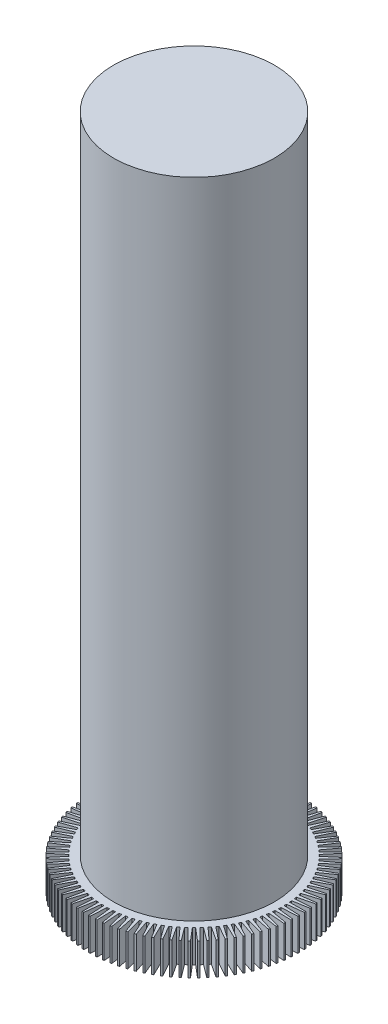
SolidWorks part; units mm, degrees
ref_plane "Front Plane" through (0, 0, 0) normal (0, 0, 1) x (1, 0, 0)
ref_plane "Top Plane" through (0, 0, 0) normal (0, 1, 0) x (1, 0, 0)
ref_plane "Right Plane" through (0, 0, 0) normal (1, 0, 0) x (0, 0, -1)
sketch "Sketch1" plane through (0, 0, 0) normal (0, 1, 0) x (1, 0, 0)
  line L0 (-0.05, 2.7495) -> (0.05, 2.7495) construction
  line L1 (0, 3.2495) -> (0, 2.2495) construction
  line L2 (-0.025, 3.2495) -> (-0.05, 2.7495)
  line L3 (0.025, 3.2495) -> (0.05, 2.7495)
  line L4 (-0.025, 3.2495) -> (0.025, 3.2495)
  line L5 (0.1791, 3.2447) -> (0.1227, 2.7473)
  line L6 (0.1791, 3.2447) -> (0.229, 3.2416)
  line L7 (0.229, 3.2416) -> (0.2225, 2.741)
  line L8 (0.3825, 3.2271) -> (0.295, 2.7341)
  line L9 (0.3825, 3.2271) -> (0.4321, 3.2208)
  line L10 (0.4321, 3.2208) -> (0.3942, 2.7216)
  line L11 (0.5843, 3.1967) -> (0.4661, 2.7102)
  line L12 (0.5843, 3.1967) -> (0.6335, 3.1873)
  line L13 (0.6335, 3.1873) -> (0.5643, 2.6915)
  line L14 (0.7839, 3.1537) -> (0.6354, 2.6756)
  line L15 (0.7839, 3.1537) -> (0.8323, 3.1412)
  line L16 (0.8323, 3.1412) -> (0.7322, 2.6507)
  line L17 (0.9804, 3.0982) -> (0.8021, 2.6304)
  line L18 (0.9804, 3.0982) -> (1.0279, 3.0828)
  line L19 (1.0279, 3.0828) -> (0.8972, 2.5995)
  line L20 (1.173, 3.0306) -> (0.9657, 2.5749)
  line L21 (1.173, 3.0306) -> (1.2195, 3.0121)
  line L22 (1.2195, 3.0121) -> (1.0587, 2.5381)
  line L23 (1.361, 2.9509) -> (1.1255, 2.5092)
  line L24 (1.361, 2.9509) -> (1.4062, 2.9296)
  line L25 (1.4062, 2.9296) -> (1.2159, 2.4666)
  line L26 (1.5436, 2.8596) -> (1.2808, 2.4335)
  line L27 (1.5436, 2.8596) -> (1.5874, 2.8356)
  line L28 (1.5874, 2.8356) -> (1.3684, 2.3854)
  line L29 (1.7201, 2.7571) -> (1.4311, 2.3483)
  line L30 (1.7201, 2.7571) -> (1.7623, 2.7303)
  line L31 (1.7623, 2.7303) -> (1.5155, 2.2947)
  line L32 (1.8898, 2.6436) -> (1.5757, 2.2538)
  line L33 (1.8898, 2.6436) -> (1.9303, 2.6142)
  line L34 (1.9303, 2.6142) -> (1.6566, 2.195)
  line L35 (2.0521, 2.5198) -> (1.7141, 2.1504)
  line L36 (2.0521, 2.5198) -> (2.0906, 2.4879)
  line L37 (2.0906, 2.4879) -> (1.7912, 2.0867)
  line L38 (2.2062, 2.3859) -> (1.8457, 2.0386)
  line L39 (2.2062, 2.3859) -> (2.2427, 2.3517)
  line L40 (2.2427, 2.3517) -> (1.9186, 1.9701)
  line L41 (2.3517, 2.2427) -> (1.9701, 1.9186)
  line L42 (2.3517, 2.2427) -> (2.3859, 2.2062)
  line L43 (2.3859, 2.2062) -> (2.0386, 1.8457)
  line L44 (2.4879, 2.0906) -> (2.0867, 1.7912)
  line L45 (2.4879, 2.0906) -> (2.5198, 2.0521)
  line L46 (2.5198, 2.0521) -> (2.1504, 1.7141)
  line L47 (2.6142, 1.9303) -> (2.195, 1.6566)
  line L48 (2.6142, 1.9303) -> (2.6436, 1.8898)
  line L49 (2.6436, 1.8898) -> (2.2538, 1.5757)
  line L50 (2.7303, 1.7623) -> (2.2947, 1.5155)
  line L51 (2.7303, 1.7623) -> (2.7571, 1.7201)
  line L52 (2.7571, 1.7201) -> (2.3483, 1.4311)
  line L53 (2.8356, 1.5874) -> (2.3854, 1.3684)
  line L54 (2.8356, 1.5874) -> (2.8596, 1.5436)
  line L55 (2.8596, 1.5436) -> (2.4335, 1.2808)
  line L56 (2.9296, 1.4062) -> (2.4666, 1.2159)
  line L57 (2.9296, 1.4062) -> (2.9509, 1.361)
  line L58 (2.9509, 1.361) -> (2.5092, 1.1255)
  line L59 (3.0121, 1.2195) -> (2.5381, 1.0587)
  line L60 (3.0121, 1.2195) -> (3.0306, 1.173)
  line L61 (3.0306, 1.173) -> (2.5749, 0.9657)
  line L62 (3.0828, 1.0279) -> (2.5995, 0.8972)
  line L63 (3.0828, 1.0279) -> (3.0982, 0.9804)
  line L64 (3.0982, 0.9804) -> (2.6304, 0.8021)
  line L65 (3.1412, 0.8323) -> (2.6507, 0.7322)
  line L66 (3.1412, 0.8323) -> (3.1537, 0.7839)
  line L67 (3.1537, 0.7839) -> (2.6756, 0.6354)
  line L68 (3.1873, 0.6335) -> (2.6915, 0.5643)
  line L69 (3.1873, 0.6335) -> (3.1967, 0.5843)
  line L70 (3.1967, 0.5843) -> (2.7102, 0.4661)
  line L71 (3.2208, 0.4321) -> (2.7216, 0.3942)
  line L72 (3.2208, 0.4321) -> (3.2271, 0.3825)
  line L73 (3.2271, 0.3825) -> (2.7341, 0.295)
  line L74 (3.2416, 0.229) -> (2.741, 0.2225)
  line L75 (3.2416, 0.229) -> (3.2447, 0.1791)
  line L76 (3.2447, 0.1791) -> (2.7473, 0.1227)
  line L77 (3.2495, 0.025) -> (2.7495, 0.05)
  line L78 (3.2495, 0.025) -> (3.2495, -0.025)
  line L79 (3.2495, -0.025) -> (2.7495, -0.05)
  line L80 (3.2447, -0.1791) -> (2.7473, -0.1227)
  line L81 (3.2447, -0.1791) -> (3.2416, -0.229)
  line L82 (3.2416, -0.229) -> (2.741, -0.2225)
  line L83 (3.2271, -0.3825) -> (2.7341, -0.295)
  line L84 (3.2271, -0.3825) -> (3.2208, -0.4321)
  line L85 (3.2208, -0.4321) -> (2.7216, -0.3942)
  line L86 (3.1967, -0.5843) -> (2.7102, -0.4661)
  line L87 (3.1967, -0.5843) -> (3.1873, -0.6335)
  line L88 (3.1873, -0.6335) -> (2.6915, -0.5643)
  line L89 (3.1537, -0.7839) -> (2.6756, -0.6354)
  line L90 (3.1537, -0.7839) -> (3.1412, -0.8323)
  line L91 (3.1412, -0.8323) -> (2.6507, -0.7322)
  line L92 (3.0982, -0.9804) -> (2.6304, -0.8021)
  line L93 (3.0982, -0.9804) -> (3.0828, -1.0279)
  line L94 (3.0828, -1.0279) -> (2.5995, -0.8972)
  line L95 (3.0306, -1.173) -> (2.5749, -0.9657)
  line L96 (3.0306, -1.173) -> (3.0121, -1.2195)
  line L97 (3.0121, -1.2195) -> (2.5381, -1.0587)
  line L98 (2.9509, -1.361) -> (2.5092, -1.1255)
  line L99 (2.9509, -1.361) -> (2.9296, -1.4062)
  line L100 (2.9296, -1.4062) -> (2.4666, -1.2159)
  line L101 (2.8596, -1.5436) -> (2.4335, -1.2808)
  line L102 (2.8596, -1.5436) -> (2.8356, -1.5874)
  line L103 (2.8356, -1.5874) -> (2.3854, -1.3684)
  line L104 (2.7571, -1.7201) -> (2.3483, -1.4311)
  line L105 (2.7571, -1.7201) -> (2.7303, -1.7623)
  line L106 (2.7303, -1.7623) -> (2.2947, -1.5155)
  line L107 (2.6436, -1.8898) -> (2.2538, -1.5757)
  line L108 (2.6436, -1.8898) -> (2.6142, -1.9303)
  line L109 (2.6142, -1.9303) -> (2.195, -1.6566)
  line L110 (2.5198, -2.0521) -> (2.1504, -1.7141)
  line L111 (2.5198, -2.0521) -> (2.4879, -2.0906)
  line L112 (2.4879, -2.0906) -> (2.0867, -1.7912)
  line L113 (2.3859, -2.2062) -> (2.0386, -1.8457)
  line L114 (2.3859, -2.2062) -> (2.3517, -2.2427)
  line L115 (2.3517, -2.2427) -> (1.9701, -1.9186)
  line L116 (2.2427, -2.3517) -> (1.9186, -1.9701)
  line L117 (2.2427, -2.3517) -> (2.2062, -2.3859)
  line L118 (2.2062, -2.3859) -> (1.8457, -2.0386)
  line L119 (2.0906, -2.4879) -> (1.7912, -2.0867)
  line L120 (2.0906, -2.4879) -> (2.0521, -2.5198)
  line L121 (2.0521, -2.5198) -> (1.7141, -2.1504)
  line L122 (1.9303, -2.6142) -> (1.6566, -2.195)
  line L123 (1.9303, -2.6142) -> (1.8898, -2.6436)
  line L124 (1.8898, -2.6436) -> (1.5757, -2.2538)
  line L125 (1.7623, -2.7303) -> (1.5155, -2.2947)
  line L126 (1.7623, -2.7303) -> (1.7201, -2.7571)
  line L127 (1.7201, -2.7571) -> (1.4311, -2.3483)
  line L128 (1.5874, -2.8356) -> (1.3684, -2.3854)
  line L129 (1.5874, -2.8356) -> (1.5436, -2.8596)
  line L130 (1.5436, -2.8596) -> (1.2808, -2.4335)
  line L131 (1.4062, -2.9296) -> (1.2159, -2.4666)
  line L132 (1.4062, -2.9296) -> (1.361, -2.9509)
  line L133 (1.361, -2.9509) -> (1.1255, -2.5092)
  line L134 (1.2195, -3.0121) -> (1.0587, -2.5381)
  line L135 (1.2195, -3.0121) -> (1.173, -3.0306)
  line L136 (1.173, -3.0306) -> (0.9657, -2.5749)
  line L137 (1.0279, -3.0828) -> (0.8972, -2.5995)
  line L138 (1.0279, -3.0828) -> (0.9804, -3.0982)
  line L139 (0.9804, -3.0982) -> (0.8021, -2.6304)
  line L140 (0.8323, -3.1412) -> (0.7322, -2.6507)
  line L141 (0.8323, -3.1412) -> (0.7839, -3.1537)
  line L142 (0.7839, -3.1537) -> (0.6354, -2.6756)
  line L143 (0.6335, -3.1873) -> (0.5643, -2.6915)
  line L144 (0.6335, -3.1873) -> (0.5843, -3.1967)
  line L145 (0.5843, -3.1967) -> (0.4661, -2.7102)
  line L146 (0.4321, -3.2208) -> (0.3942, -2.7216)
  line L147 (0.4321, -3.2208) -> (0.3825, -3.2271)
  line L148 (0.3825, -3.2271) -> (0.295, -2.7341)
  line L149 (0.229, -3.2416) -> (0.2225, -2.741)
  line L150 (0.229, -3.2416) -> (0.1791, -3.2447)
  line L151 (0.1791, -3.2447) -> (0.1227, -2.7473)
  line L152 (0.025, -3.2495) -> (0.05, -2.7495)
  line L153 (0.025, -3.2495) -> (-0.025, -3.2495)
  line L154 (-0.025, -3.2495) -> (-0.05, -2.7495)
  line L155 (-0.1791, -3.2447) -> (-0.1227, -2.7473)
  line L156 (-0.1791, -3.2447) -> (-0.229, -3.2416)
  line L157 (-0.229, -3.2416) -> (-0.2225, -2.741)
  line L158 (-0.3825, -3.2271) -> (-0.295, -2.7341)
  line L159 (-0.3825, -3.2271) -> (-0.4321, -3.2208)
  line L160 (-0.4321, -3.2208) -> (-0.3942, -2.7216)
  line L161 (-0.5843, -3.1967) -> (-0.4661, -2.7102)
  line L162 (-0.5843, -3.1967) -> (-0.6335, -3.1873)
  line L163 (-0.6335, -3.1873) -> (-0.5643, -2.6915)
  line L164 (-0.7839, -3.1537) -> (-0.6354, -2.6756)
  line L165 (-0.7839, -3.1537) -> (-0.8323, -3.1412)
  line L166 (-0.8323, -3.1412) -> (-0.7322, -2.6507)
  line L167 (-0.9804, -3.0982) -> (-0.8021, -2.6304)
  line L168 (-0.9804, -3.0982) -> (-1.0279, -3.0828)
  line L169 (-1.0279, -3.0828) -> (-0.8972, -2.5995)
  line L170 (-1.173, -3.0306) -> (-0.9657, -2.5749)
  line L171 (-1.173, -3.0306) -> (-1.2195, -3.0121)
  line L172 (-1.2195, -3.0121) -> (-1.0587, -2.5381)
  line L173 (-1.361, -2.9509) -> (-1.1255, -2.5092)
  line L174 (-1.361, -2.9509) -> (-1.4062, -2.9296)
  line L175 (-1.4062, -2.9296) -> (-1.2159, -2.4666)
  line L176 (-1.5436, -2.8596) -> (-1.2808, -2.4335)
  line L177 (-1.5436, -2.8596) -> (-1.5874, -2.8356)
  line L178 (-1.5874, -2.8356) -> (-1.3684, -2.3854)
  line L179 (-1.7201, -2.7571) -> (-1.4311, -2.3483)
  line L180 (-1.7201, -2.7571) -> (-1.7623, -2.7303)
  line L181 (-1.7623, -2.7303) -> (-1.5155, -2.2947)
  line L182 (-1.8898, -2.6436) -> (-1.5757, -2.2538)
  line L183 (-1.8898, -2.6436) -> (-1.9303, -2.6142)
  line L184 (-1.9303, -2.6142) -> (-1.6566, -2.195)
  line L185 (-2.0521, -2.5198) -> (-1.7141, -2.1504)
  line L186 (-2.0521, -2.5198) -> (-2.0906, -2.4879)
  line L187 (-2.0906, -2.4879) -> (-1.7912, -2.0867)
  line L188 (-2.2062, -2.3859) -> (-1.8457, -2.0386)
  line L189 (-2.2062, -2.3859) -> (-2.2427, -2.3517)
  line L190 (-2.2427, -2.3517) -> (-1.9186, -1.9701)
  line L191 (-2.3517, -2.2427) -> (-1.9701, -1.9186)
  line L192 (-2.3517, -2.2427) -> (-2.3859, -2.2062)
  line L193 (-2.3859, -2.2062) -> (-2.0386, -1.8457)
  line L194 (-2.4879, -2.0906) -> (-2.0867, -1.7912)
  line L195 (-2.4879, -2.0906) -> (-2.5198, -2.0521)
  line L196 (-2.5198, -2.0521) -> (-2.1504, -1.7141)
  line L197 (-2.6142, -1.9303) -> (-2.195, -1.6566)
  line L198 (-2.6142, -1.9303) -> (-2.6436, -1.8898)
  line L199 (-2.6436, -1.8898) -> (-2.2538, -1.5757)
  line L200 (-2.7303, -1.7623) -> (-2.2947, -1.5155)
  line L201 (-2.7303, -1.7623) -> (-2.7571, -1.7201)
  line L202 (-2.7571, -1.7201) -> (-2.3483, -1.4311)
  line L203 (-2.8356, -1.5874) -> (-2.3854, -1.3684)
  line L204 (-2.8356, -1.5874) -> (-2.8596, -1.5436)
  line L205 (-2.8596, -1.5436) -> (-2.4335, -1.2808)
  line L206 (-2.9296, -1.4062) -> (-2.4666, -1.2159)
  line L207 (-2.9296, -1.4062) -> (-2.9509, -1.361)
  line L208 (-2.9509, -1.361) -> (-2.5092, -1.1255)
  line L209 (-3.0121, -1.2195) -> (-2.5381, -1.0587)
  line L210 (-3.0121, -1.2195) -> (-3.0306, -1.173)
  line L211 (-3.0306, -1.173) -> (-2.5749, -0.9657)
  line L212 (-3.0828, -1.0279) -> (-2.5995, -0.8972)
  line L213 (-3.0828, -1.0279) -> (-3.0982, -0.9804)
  line L214 (-3.0982, -0.9804) -> (-2.6304, -0.8021)
  line L215 (-3.1412, -0.8323) -> (-2.6507, -0.7322)
  line L216 (-3.1412, -0.8323) -> (-3.1537, -0.7839)
  line L217 (-3.1537, -0.7839) -> (-2.6756, -0.6354)
  line L218 (-3.1873, -0.6335) -> (-2.6915, -0.5643)
  line L219 (-3.1873, -0.6335) -> (-3.1967, -0.5843)
  line L220 (-3.1967, -0.5843) -> (-2.7102, -0.4661)
  line L221 (-3.2208, -0.4321) -> (-2.7216, -0.3942)
  line L222 (-3.2208, -0.4321) -> (-3.2271, -0.3825)
  line L223 (-3.2271, -0.3825) -> (-2.7341, -0.295)
  line L224 (-3.2416, -0.229) -> (-2.741, -0.2225)
  line L225 (-3.2416, -0.229) -> (-3.2447, -0.1791)
  line L226 (-3.2447, -0.1791) -> (-2.7473, -0.1227)
  line L227 (-3.2495, -0.025) -> (-2.7495, -0.05)
  line L228 (-3.2495, -0.025) -> (-3.2495, 0.025)
  line L229 (-3.2495, 0.025) -> (-2.7495, 0.05)
  line L230 (-3.2447, 0.1791) -> (-2.7473, 0.1227)
  line L231 (-3.2447, 0.1791) -> (-3.2416, 0.229)
  line L232 (-3.2416, 0.229) -> (-2.741, 0.2225)
  line L233 (-3.2271, 0.3825) -> (-2.7341, 0.295)
  line L234 (-3.2271, 0.3825) -> (-3.2208, 0.4321)
  line L235 (-3.2208, 0.4321) -> (-2.7216, 0.3942)
  line L236 (-3.1967, 0.5843) -> (-2.7102, 0.4661)
  line L237 (-3.1967, 0.5843) -> (-3.1873, 0.6335)
  line L238 (-3.1873, 0.6335) -> (-2.6915, 0.5643)
  line L239 (-3.1537, 0.7839) -> (-2.6756, 0.6354)
  line L240 (-3.1537, 0.7839) -> (-3.1412, 0.8323)
  line L241 (-3.1412, 0.8323) -> (-2.6507, 0.7322)
  line L242 (-3.0982, 0.9804) -> (-2.6304, 0.8021)
  line L243 (-3.0982, 0.9804) -> (-3.0828, 1.0279)
  line L244 (-3.0828, 1.0279) -> (-2.5995, 0.8972)
  line L245 (-3.0306, 1.173) -> (-2.5749, 0.9657)
  line L246 (-3.0306, 1.173) -> (-3.0121, 1.2195)
  line L247 (-3.0121, 1.2195) -> (-2.5381, 1.0587)
  line L248 (-2.9509, 1.361) -> (-2.5092, 1.1255)
  line L249 (-2.9509, 1.361) -> (-2.9296, 1.4062)
  line L250 (-2.9296, 1.4062) -> (-2.4666, 1.2159)
  line L251 (-2.8596, 1.5436) -> (-2.4335, 1.2808)
  line L252 (-2.8596, 1.5436) -> (-2.8356, 1.5874)
  line L253 (-2.8356, 1.5874) -> (-2.3854, 1.3684)
  line L254 (-2.7571, 1.7201) -> (-2.3483, 1.4311)
  line L255 (-2.7571, 1.7201) -> (-2.7303, 1.7623)
  line L256 (-2.7303, 1.7623) -> (-2.2947, 1.5155)
  line L257 (-2.6436, 1.8898) -> (-2.2538, 1.5757)
  line L258 (-2.6436, 1.8898) -> (-2.6142, 1.9303)
  line L259 (-2.6142, 1.9303) -> (-2.195, 1.6566)
  line L260 (-2.5198, 2.0521) -> (-2.1504, 1.7141)
  line L261 (-2.5198, 2.0521) -> (-2.4879, 2.0906)
  line L262 (-2.4879, 2.0906) -> (-2.0867, 1.7912)
  line L263 (-2.3859, 2.2062) -> (-2.0386, 1.8457)
  line L264 (-2.3859, 2.2062) -> (-2.3517, 2.2427)
  line L265 (-2.3517, 2.2427) -> (-1.9701, 1.9186)
  line L266 (-2.2427, 2.3517) -> (-1.9186, 1.9701)
  line L267 (-2.2427, 2.3517) -> (-2.2062, 2.3859)
  line L268 (-2.2062, 2.3859) -> (-1.8457, 2.0386)
  line L269 (-2.0906, 2.4879) -> (-1.7912, 2.0867)
  line L270 (-2.0906, 2.4879) -> (-2.0521, 2.5198)
  line L271 (-2.0521, 2.5198) -> (-1.7141, 2.1504)
  line L272 (-1.9303, 2.6142) -> (-1.6566, 2.195)
  line L273 (-1.9303, 2.6142) -> (-1.8898, 2.6436)
  line L274 (-1.8898, 2.6436) -> (-1.5757, 2.2538)
  line L275 (-1.7623, 2.7303) -> (-1.5155, 2.2947)
  line L276 (-1.7623, 2.7303) -> (-1.7201, 2.7571)
  line L277 (-1.7201, 2.7571) -> (-1.4311, 2.3483)
  line L278 (-1.5874, 2.8356) -> (-1.3684, 2.3854)
  line L279 (-1.5874, 2.8356) -> (-1.5436, 2.8596)
  line L280 (-1.5436, 2.8596) -> (-1.2808, 2.4335)
  line L281 (-1.4062, 2.9296) -> (-1.2159, 2.4666)
  line L282 (-1.4062, 2.9296) -> (-1.361, 2.9509)
  line L283 (-1.361, 2.9509) -> (-1.1255, 2.5092)
  line L284 (-1.2195, 3.0121) -> (-1.0587, 2.5381)
  line L285 (-1.2195, 3.0121) -> (-1.173, 3.0306)
  line L286 (-1.173, 3.0306) -> (-0.9657, 2.5749)
  line L287 (-1.0279, 3.0828) -> (-0.8972, 2.5995)
  line L288 (-1.0279, 3.0828) -> (-0.9804, 3.0982)
  line L289 (-0.9804, 3.0982) -> (-0.8021, 2.6304)
  line L290 (-0.8323, 3.1412) -> (-0.7322, 2.6507)
  line L291 (-0.8323, 3.1412) -> (-0.7839, 3.1537)
  line L292 (-0.7839, 3.1537) -> (-0.6354, 2.6756)
  line L293 (-0.6335, 3.1873) -> (-0.5643, 2.6915)
  line L294 (-0.6335, 3.1873) -> (-0.5843, 3.1967)
  line L295 (-0.5843, 3.1967) -> (-0.4661, 2.7102)
  line L296 (-0.4321, 3.2208) -> (-0.3942, 2.7216)
  line L297 (-0.4321, 3.2208) -> (-0.3825, 3.2271)
  line L298 (-0.3825, 3.2271) -> (-0.295, 2.7341)
  line L299 (-0.229, 3.2416) -> (-0.2225, 2.741)
  line L300 (-0.229, 3.2416) -> (-0.1791, 3.2447)
  line L301 (-0.1791, 3.2447) -> (-0.1227, 2.7473)
  arc A0 (-1.9186, 1.9701) -> (-1.9701, 1.9186) centre (0, 0) ccw
  arc A1 (-1.7912, 2.0867) -> (-1.8457, 2.0386) centre (0, 0) ccw
  arc A2 (-1.6566, 2.195) -> (-1.7141, 2.1504) centre (0, 0) ccw
  arc A3 (-1.5155, 2.2947) -> (-1.5757, 2.2538) centre (0, 0) ccw
  arc A4 (-1.3684, 2.3854) -> (-1.4311, 2.3483) centre (0, 0) ccw
  arc A5 (-1.2159, 2.4666) -> (-1.2808, 2.4335) centre (0, 0) ccw
  arc A6 (-1.0587, 2.5381) -> (-1.1255, 2.5092) centre (0, 0) ccw
  arc A7 (-0.8972, 2.5995) -> (-0.9657, 2.5749) centre (0, 0) ccw
  arc A8 (-0.7322, 2.6507) -> (-0.8021, 2.6304) centre (0, 0) ccw
  arc A9 (-0.5643, 2.6915) -> (-0.6354, 2.6756) centre (0, 0) ccw
  arc A10 (-0.3942, 2.7216) -> (-0.4661, 2.7102) centre (0, 0) ccw
  arc A11 (-0.2225, 2.741) -> (-0.295, 2.7341) centre (0, 0) ccw
  arc A12 (0.1227, 2.7473) -> (0.05, 2.7495) centre (0, 0) ccw
  arc A13 (0.295, 2.7341) -> (0.2225, 2.741) centre (0, 0) ccw
  arc A14 (0.4661, 2.7102) -> (0.3942, 2.7216) centre (0, 0) ccw
  arc A15 (0.6354, 2.6756) -> (0.5643, 2.6915) centre (0, 0) ccw
  arc A16 (0.8021, 2.6304) -> (0.7322, 2.6507) centre (0, 0) ccw
  arc A17 (0.9657, 2.5749) -> (0.8972, 2.5995) centre (0, 0) ccw
  arc A18 (1.1255, 2.5092) -> (1.0587, 2.5381) centre (0, 0) ccw
  arc A19 (1.2808, 2.4335) -> (1.2159, 2.4666) centre (0, 0) ccw
  arc A20 (1.4311, 2.3483) -> (1.3684, 2.3854) centre (0, 0) ccw
  arc A21 (1.5757, 2.2538) -> (1.5155, 2.2947) centre (0, 0) ccw
  arc A22 (1.7141, 2.1504) -> (1.6566, 2.195) centre (0, 0) ccw
  arc A23 (1.8457, 2.0386) -> (1.7912, 2.0867) centre (0, 0) ccw
  arc A24 (1.9701, 1.9186) -> (1.9186, 1.9701) centre (0, 0) ccw
  arc A25 (2.0867, 1.7912) -> (2.0386, 1.8457) centre (0, 0) ccw
  arc A26 (2.195, 1.6566) -> (2.1504, 1.7141) centre (0, 0) ccw
  arc A27 (2.2947, 1.5155) -> (2.2538, 1.5757) centre (0, 0) ccw
  arc A28 (2.3854, 1.3684) -> (2.3483, 1.4311) centre (0, 0) ccw
  arc A29 (2.4666, 1.2159) -> (2.4335, 1.2808) centre (0, 0) ccw
  arc A30 (2.5381, 1.0587) -> (2.5092, 1.1255) centre (0, 0) ccw
  arc A31 (2.5995, 0.8972) -> (2.5749, 0.9657) centre (0, 0) ccw
  arc A32 (2.6507, 0.7322) -> (2.6304, 0.8021) centre (0, 0) ccw
  arc A33 (2.6915, 0.5643) -> (2.6756, 0.6354) centre (0, 0) ccw
  arc A34 (2.7216, 0.3942) -> (2.7102, 0.4661) centre (0, 0) ccw
  arc A35 (2.741, 0.2225) -> (2.7341, 0.295) centre (0, 0) ccw
  arc A36 (2.7495, 0.05) -> (2.7473, 0.1227) centre (0, 0) ccw
  arc A37 (2.7473, -0.1227) -> (2.7495, -0.05) centre (0, 0) ccw
  arc A38 (2.7341, -0.295) -> (2.741, -0.2225) centre (0, 0) ccw
  arc A39 (2.7102, -0.4661) -> (2.7216, -0.3942) centre (0, 0) ccw
  arc A40 (2.6756, -0.6354) -> (2.6915, -0.5643) centre (0, 0) ccw
  arc A41 (2.6304, -0.8021) -> (2.6507, -0.7322) centre (0, 0) ccw
  arc A42 (2.5749, -0.9657) -> (2.5995, -0.8972) centre (0, 0) ccw
  arc A43 (2.5092, -1.1255) -> (2.5381, -1.0587) centre (0, 0) ccw
  arc A44 (2.4335, -1.2808) -> (2.4666, -1.2159) centre (0, 0) ccw
  arc A45 (2.3483, -1.4311) -> (2.3854, -1.3684) centre (0, 0) ccw
  arc A46 (2.2538, -1.5757) -> (2.2947, -1.5155) centre (0, 0) ccw
  arc A47 (2.0386, -1.8457) -> (2.0867, -1.7912) centre (0, 0) ccw
  arc A48 (2.1504, -1.7141) -> (2.195, -1.6566) centre (0, 0) ccw
  arc A49 (1.7912, -2.0867) -> (1.8457, -2.0386) centre (0, 0) ccw
  arc A50 (1.3684, -2.3854) -> (1.4311, -2.3483) centre (0, 0) ccw
  arc A51 (1.5155, -2.2947) -> (1.5757, -2.2538) centre (0, 0) ccw
  arc A52 (1.6566, -2.195) -> (1.7141, -2.1504) centre (0, 0) ccw
  arc A53 (1.2159, -2.4666) -> (1.2808, -2.4335) centre (0, 0) ccw
  arc A54 (1.0587, -2.5381) -> (1.1255, -2.5092) centre (0, 0) ccw
  arc A55 (0.8972, -2.5995) -> (0.9657, -2.5749) centre (0, 0) ccw
  arc A56 (0.7322, -2.6507) -> (0.8021, -2.6304) centre (0, 0) ccw
  arc A57 (0.5643, -2.6915) -> (0.6354, -2.6756) centre (0, 0) ccw
  arc A58 (0.3942, -2.7216) -> (0.4661, -2.7102) centre (0, 0) ccw
  arc A59 (0.2225, -2.741) -> (0.295, -2.7341) centre (0, 0) ccw
  arc A60 (0.05, -2.7495) -> (0.1227, -2.7473) centre (0, 0) ccw
  arc A61 (-0.1227, -2.7473) -> (-0.05, -2.7495) centre (0, 0) ccw
  arc A62 (-0.295, -2.7341) -> (-0.2225, -2.741) centre (0, 0) ccw
  arc A63 (-0.4661, -2.7102) -> (-0.3942, -2.7216) centre (0, 0) ccw
  arc A64 (-0.6354, -2.6756) -> (-0.5643, -2.6915) centre (0, 0) ccw
  arc A65 (-2.0386, 1.8457) -> (-2.0867, 1.7912) centre (0, 0) ccw
  arc A66 (-2.1504, 1.7141) -> (-2.195, 1.6566) centre (0, 0) ccw
  arc A67 (-2.2538, 1.5757) -> (-2.2947, 1.5155) centre (0, 0) ccw
  arc A68 (-2.3483, 1.4311) -> (-2.3854, 1.3684) centre (0, 0) ccw
  arc A69 (-2.4335, 1.2808) -> (-2.4666, 1.2159) centre (0, 0) ccw
  arc A70 (-2.5092, 1.1255) -> (-2.5381, 1.0587) centre (0, 0) ccw
  arc A71 (-2.5749, 0.9657) -> (-2.5995, 0.8972) centre (0, 0) ccw
  arc A72 (-2.6304, 0.8021) -> (-2.6507, 0.7322) centre (0, 0) ccw
  arc A73 (-2.6756, 0.6354) -> (-2.6915, 0.5643) centre (0, 0) ccw
  arc A74 (-2.7102, 0.4661) -> (-2.7216, 0.3942) centre (0, 0) ccw
  arc A75 (-2.7341, 0.295) -> (-2.741, 0.2225) centre (0, 0) ccw
  arc A76 (-2.7473, 0.1227) -> (-2.7495, 0.05) centre (0, 0) ccw
  arc A77 (-2.7495, -0.05) -> (-2.7473, -0.1227) centre (0, 0) ccw
  arc A78 (-2.741, -0.2225) -> (-2.7341, -0.295) centre (0, 0) ccw
  arc A79 (-2.7216, -0.3942) -> (-2.7102, -0.4661) centre (0, 0) ccw
  arc A80 (-2.6915, -0.5643) -> (-2.6756, -0.6354) centre (0, 0) ccw
  arc A81 (-2.6507, -0.7322) -> (-2.6304, -0.8021) centre (0, 0) ccw
  arc A82 (-2.5995, -0.8972) -> (-2.5749, -0.9657) centre (0, 0) ccw
  arc A83 (-2.5381, -1.0587) -> (-2.5092, -1.1255) centre (0, 0) ccw
  arc A84 (-2.4666, -1.2159) -> (-2.4335, -1.2808) centre (0, 0) ccw
  arc A85 (-2.2947, -1.5155) -> (-2.2538, -1.5757) centre (0, 0) ccw
  arc A86 (-2.3854, -1.3684) -> (-2.3483, -1.4311) centre (0, 0) ccw
  arc A87 (-2.195, -1.6566) -> (-2.1504, -1.7141) centre (0, 0) ccw
  arc A88 (-2.0867, -1.7912) -> (-2.0386, -1.8457) centre (0, 0) ccw
  arc A89 (-1.9701, -1.9186) -> (-1.9186, -1.9701) centre (0, 0) ccw
  arc A90 (-1.8457, -2.0386) -> (-1.7912, -2.0867) centre (0, 0) ccw
  arc A91 (-1.7141, -2.1504) -> (-1.6566, -2.195) centre (0, 0) ccw
  arc A92 (-1.5757, -2.2538) -> (-1.5155, -2.2947) centre (0, 0) ccw
  arc A93 (-1.4311, -2.3483) -> (-1.3684, -2.3854) centre (0, 0) ccw
  arc A94 (-0.8021, -2.6304) -> (-0.7322, -2.6507) centre (0, 0) ccw
  arc A95 (-0.9657, -2.5749) -> (-0.8972, -2.5995) centre (0, 0) ccw
  arc A96 (-1.1255, -2.5092) -> (-1.0587, -2.5381) centre (0, 0) ccw
  arc A97 (-1.2808, -2.4335) -> (-1.2159, -2.4666) centre (0, 0) ccw
  arc A98 (-0.05, 2.7495) -> (-0.1227, 2.7473) centre (0, 0) ccw
  arc A99 (1.9186, -1.9701) -> (1.9701, -1.9186) centre (0, 0) ccw
  point P8 (0, 2.7495)
  point P409 (0, 0)
  dimension "D3" = 100
extrude "Boss-Extrude2" add sketch "Sketch1" along normal blind 1
sketch "Sketch2" plane through (0, 1, 0) normal (0, 1, 0) x (1, 0, 0)
  circle A0 centre (0, 0) radius 2.5
  dimension "D1" = 5
extrude "Boss-Extrude3" add sketch "Sketch2" along normal blind 20
cosmetic thread "Cosmetic Thread1" parameters "D2"=4
